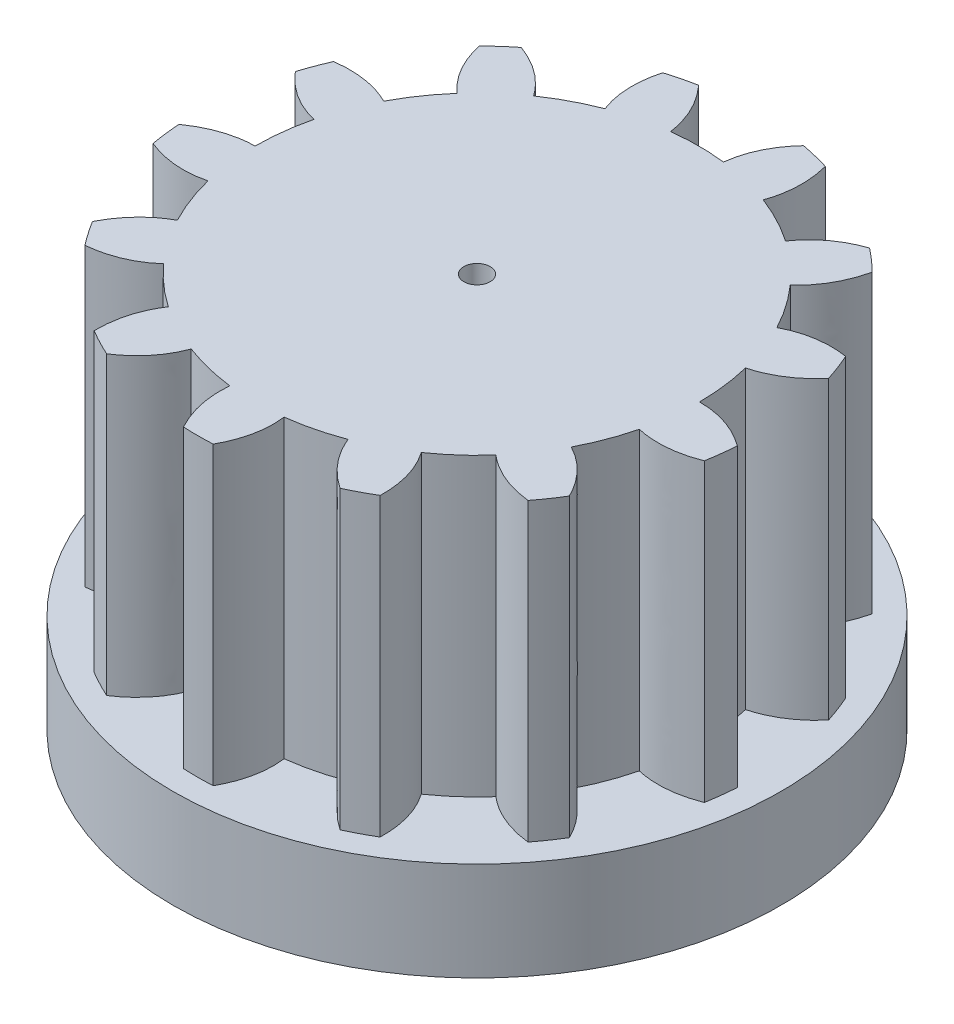
SolidWorks part; units mm, degrees
ref_plane "Front Plane" through (0, 0, 0) normal (0, 0, 1) x (1, 0, 0)
ref_plane "Top Plane" through (0, 0, 0) normal (0, 1, 0) x (1, 0, 0)
ref_plane "Right Plane" through (0, 0, 0) normal (1, 0, 0) x (0, 0, -1)
sketch "Sketch1" plane through (0, 0, 0) normal (0, 1, 0) x (1, 0, 0)
  line L0 (0, 0) -> (0, 17.0926) construction
  line L1 (0, 0) -> (3.5061, 14.2208) construction
  line L2 (0, 0) -> (1.9234, 15.8361) construction
  line L3 (0, 0) -> (4.6786, 12.3295) construction
  circle A3 centre (0, 0) radius 0.4
  arc A4 (-5.0652, 4.4616) -> (-5.9762, 3.138) centre (0, 0) ccw
  arc A6 (-2.4116, 6.3045) -> (-3.8334, 5.5559) centre (0, 0) ccw
  arc A7 (0.8138, 6.7008) -> (-0.8124, 6.7009) centre (0, 0) ccw
  arc A8 (3.8185, 5.5661) -> (2.3948, 6.3109) centre (0, 0) ccw
  arc A9 (5.9678, 3.154) -> (5.0533, 4.4751) centre (0, 0) ccw
  arc A10 (6.75, 0.0193) -> (6.5542, 1.6141) centre (0, 0) ccw
  arc A11 (5.9858, -3.1198) -> (6.5536, -1.6166) centre (0, 0) ccw
  arc A12 (3.8503, -5.5442) -> (5.0516, -4.477) centre (0, 0) ccw
  arc A13 (0.8328, -6.6984) -> (2.3924, -6.3118) centre (0, 0) ccw
  arc A14 (-2.3755, -6.3182) -> (-0.8149, -6.7006) centre (0, 0) ccw
  arc A15 (-5.0396, -4.4905) -> (-3.8355, -5.5544) centre (0, 0) ccw
  arc A16 (-6.5492, -1.6341) -> (-5.9774, -3.1358) centre (0, 0) ccw
  arc A17 (-6.5585, 1.5966) -> (-6.75, 0.0013) centre (0, 0) ccw
  arc A18 (-7.781, 3.4215) -> (-8.1003, 2.5759) centre (0, 0) ccw
  arc A19 (-8.4797, -0.5864) -> (-8.3695, -1.4836) centre (0, 0) ccw
  arc A20 (-7.2359, -4.46) -> (-6.7214, -5.2032) centre (0, 0) ccw
  arc A21 (-4.3344, -7.3118) -> (-3.5335, -7.7308) centre (0, 0) ccw
  arc A22 (-5.2996, 6.6456) -> (-5.9754, 6.0452) centre (0, 0) ccw
  arc A23 (-1.6043, 8.3472) -> (-2.4816, 8.1297) centre (0, 0) ccw
  arc A24 (8.3737, -1.46) -> (8.4814, -0.5625) centre (0, 0) ccw
  arc A25 (8.093, 2.5987) -> (7.7713, 3.4434) centre (0, 0) ccw
  arc A28 (2.4587, 8.1366) -> (1.5807, 8.3517) centre (0, 0) ccw
  arc A31 (5.9583, 6.062) -> (5.2809, 6.6605) centre (0, 0) ccw
  arc A32 (6.736, -5.1842) -> (7.2485, -4.4396) centre (0, 0) ccw
  arc A33 (3.5553, -7.7208) -> (4.355, -7.2996) centre (0, 0) ccw
  arc A34 (-0.44, -8.4886) -> (0.4639, -8.4873) centre (0, 0) ccw
  spline S0 degree 3 poles (0.633, 5.2117) (0.7252, 5.9828) (1.0144, 6.8191) (1.6201, 7.3229) knots 0 0 0 0 1 1 1 1 construction
  spline S1 degree 1 poles (1.6201, 7.3229) (1.9696, 7.2368) knots 0 0 1 1 construction
  spline S2 degree 3 poles (1.8622, 4.9086) (2.139, 5.6342) (2.2717, 6.5091) (1.9696, 7.2368) knots 0 0 0 0 1 1 1 1 construction
  spline S3 degree 3 poles (3.93, 3.481) (4.5123, 3.9948) (5.0364, 4.7079) (5.1071, 5.4925) knots 0 0 0 0 1 1 1 1 construction
  spline S4 degree 3 poles (2.9825, 4.3206) (3.4225, 4.9605) (4.0672, 5.5666) (4.8376, 5.7313) knots 0 0 0 0 1 1 1 1 construction
  spline S5 degree 1 poles (4.8376, 5.7313) (5.1071, 5.4925) knots 0 0 1 1 construction
  spline S6 degree 3 poles (5.0976, 1.2559) (5.852, 1.4403) (6.6474, 1.8281) (7.0746, 2.49) knots 0 0 0 0 1 1 1 1 construction
  spline S7 degree 3 poles (4.6487, 2.4397) (5.3357, 2.8018) (6.1883, 3.0389) (6.947, 2.8266) knots 0 0 0 0 1 1 1 1 construction
  spline S8 degree 1 poles (6.947, 2.8266) (7.0746, 2.49) knots 0 0 1 1 construction
  spline S9 degree 3 poles (5.0973, -1.2569) (5.851, -1.4442) (6.7355, -1.4705) (7.4214, -1.083) knots 0 0 0 0 1 1 1 1 construction
  spline S10 degree 3 poles (5.25, -0.0002) (6.0266, 0.0012) (6.8917, -0.1851) (7.4648, -0.7256) knots 0 0 0 0 1 1 1 1 construction
  spline S11 degree 1 poles (7.4648, -0.7256) (7.4214, -1.083) knots 0 0 1 1 construction
  spline S12 degree 3 poles (3.9293, -3.4818) (4.5096, -3.9979) (5.2806, -4.4322) (6.068, -4.4078) knots 0 0 0 0 1 1 1 1 construction
  spline S13 degree 3 poles (4.6486, -2.4399) (5.3369, -2.7996) (6.0163, -3.3666) (6.2726, -4.1115) knots 0 0 0 0 1 1 1 1 construction
  spline S14 degree 1 poles (6.2726, -4.1115) (6.068, -4.4078) knots 0 0 1 1 construction
  spline S15 degree 3 poles (1.8612, -4.909) (2.1351, -5.6357) (2.616, -6.3786) (3.3246, -6.7229) knots 0 0 0 0 1 1 1 1 construction
  spline S16 degree 3 poles (2.9822, -4.3208) (3.4245, -4.9591) (3.7626, -5.7769) (3.6434, -6.5556) knots 0 0 0 0 1 1 1 1 construction
  spline S17 degree 1 poles (3.6434, -6.5556) (3.3246, -6.7229) knots 0 0 1 1 construction
  spline S18 degree 3 poles (-0.6334, -5.2117) (-0.7285, -5.9824) (-0.6479, -6.8636) (-0.1805, -7.4978) knots 0 0 0 0 1 1 1 1 construction
  spline S19 degree 3 poles (0.6327, -5.2117) (0.7277, -5.9825) (0.647, -6.8637) (0.1795, -7.4979) knots 0 0 0 0 1 1 1 1 construction
  spline S20 degree 1 poles (0.1795, -7.4979) (-0.1805, -7.4978) knots 0 0 1 1 construction
  spline S21 degree 3 poles (-2.9828, -4.3204) (-3.4252, -4.9586) (-3.7634, -5.7764) (-3.6443, -6.5551) knots 0 0 0 0 1 1 1 1 construction
  spline S22 degree 3 poles (-1.8618, -4.9088) (-2.1359, -5.6354) (-2.6168, -6.3782) (-3.3255, -6.7224) knots 0 0 0 0 1 1 1 1 construction
  spline S23 degree 1 poles (-3.3255, -6.7224) (-3.6443, -6.5551) knots 0 0 1 1 construction
  spline S24 degree 3 poles (-4.6489, -2.4393) (-5.3372, -2.7989) (-6.0167, -3.3658) (-6.2731, -4.1107) knots 0 0 0 0 1 1 1 1 construction
  spline S25 degree 3 poles (-3.9298, -3.4813) (-4.5101, -3.9973) (-5.2812, -4.4315) (-6.0686, -4.407) knots 0 0 0 0 1 1 1 1 construction
  spline S26 degree 1 poles (-6.0686, -4.407) (-6.2731, -4.1107) knots 0 0 1 1 construction
  spline S27 degree 3 poles (-5.25, 0.0006) (-6.0266, 0.0021) (-6.8917, -0.1841) (-7.4649, -0.7246) knots 0 0 0 0 1 1 1 1 construction
  spline S28 degree 3 poles (-5.0975, -1.2563) (-5.8512, -1.4435) (-6.7357, -1.4696) (-7.4215, -1.082) knots 0 0 0 0 1 1 1 1 construction
  spline S29 degree 1 poles (-7.4215, -1.082) (-7.4649, -0.7246) knots 0 0 1 1 construction
  spline S30 degree 3 poles (-4.6484, 2.4403) (-5.3353, 2.8025) (-6.1879, 3.0397) (-6.9466, 2.8276) knots 0 0 0 0 1 1 1 1 construction
  spline S31 degree 3 poles (-5.0974, 1.2566) (-5.8518, 1.441) (-6.6471, 1.829) (-7.0743, 2.4909) knots 0 0 0 0 1 1 1 1 construction
  spline S32 degree 1 poles (-7.0743, 2.4909) (-6.9466, 2.8276) knots 0 0 1 1 construction
  spline S33 degree 3 poles (-2.9819, 4.321) (-3.4218, 4.9609) (-4.0665, 5.5672) (-4.8369, 5.7319) knots 0 0 0 0 1 1 1 1 construction
  spline S34 degree 3 poles (-3.9296, 3.4815) (-4.5118, 3.9954) (-5.0358, 4.7085) (-5.1064, 5.4932) knots 0 0 0 0 1 1 1 1 construction
  spline S35 degree 1 poles (-5.1064, 5.4932) (-4.8369, 5.7319) knots 0 0 1 1 construction
  spline S36 degree 3 poles (-0.6323, 5.2118) (-0.7244, 5.9829) (-1.0135, 6.8193) (-1.6191, 7.3232) knots 0 0 0 0 1 1 1 1 construction
  spline S37 degree 3 poles (-1.8615, 4.9089) (-2.1382, 5.6345) (-2.2708, 6.5094) (-1.9686, 7.237) knots 0 0 0 0 1 1 1 1 construction
  spline S38 degree 1 poles (-1.9686, 7.237) (-1.6191, 7.3232) knots 0 0 1 1 construction
  spline S39 degree 3 poles (-4.6484, 2.4403) (-4.4519, 2.8146) (-4.2099, 3.1651) (-3.9296, 3.4815) knots 0 0 0 0 0.038449 0.038449 0.038449 0.038449 construction
  spline S40 degree 3 poles (-2.9819, 4.321) (-2.6339, 4.5611) (-2.2568, 4.759) (-1.8615, 4.9089) knots 0.076923 0.076923 0.076923 0.076923 0.115372 0.115372 0.115372 0.115372 construction
  spline S41 degree 3 poles (-0.6323, 5.2118) (-0.2126, 5.2627) (0.2133, 5.2627) (0.633, 5.2117) (0.633, 5.2117) knots 0.153846 0.153846 0.153846 0.153846 0.192296 0.192296 0.192296 0.192296 0.192296 construction
  spline S42 degree 3 poles (-5.25, 0.0006) (-5.25, 0.4233) (-5.1986, 0.8461) (-5.0974, 1.2566) knots 0.923077 0.923077 0.923077 0.923077 0.961526 0.961526 0.961526 0.961526 construction
  spline S43 degree 3 poles (-4.6489, -2.4393) (-4.8453, -2.0649) (-4.9963, -1.6667) (-5.0975, -1.2563) knots 0.846154 0.846154 0.846154 0.846154 0.884603 0.884603 0.884603 0.884603 construction
  spline S44 degree 3 poles (-2.9828, -4.3204) (-3.3307, -4.0802) (-3.6494, -3.7977) (-3.9298, -3.4813) knots 0.769231 0.769231 0.769231 0.769231 0.80768 0.80768 0.80768 0.80768 construction
  spline S45 degree 3 poles (-0.6334, -5.2117) (-1.053, -5.1607) (-1.4665, -5.0587) (-1.8618, -4.9088) knots 0.692308 0.692308 0.692308 0.692308 0.730757 0.730757 0.730757 0.730757 construction
  spline S46 degree 3 poles (1.8612, -4.909) (1.4659, -5.0589) (1.0524, -5.1608) (0.6327, -5.2117) knots 0.615385 0.615385 0.615385 0.615385 0.653834 0.653834 0.653834 0.653834 construction
  spline S47 degree 3 poles (3.9293, -3.4818) (3.6489, -3.7982) (3.3302, -4.0806) (2.9822, -4.3208) knots 0.538462 0.538462 0.538462 0.538462 0.576911 0.576911 0.576911 0.576911 construction
  spline S48 degree 3 poles (5.0973, -1.2569) (4.9961, -1.6674) (4.8451, -2.0656) (4.6486, -2.4399) knots 0.461538 0.461538 0.461538 0.461538 0.499988 0.499988 0.499988 0.499988 construction
  spline S49 degree 3 poles (5.0976, 1.2559) (5.1987, 0.8454) (5.25, 0.4226) (5.25, -0.0002) knots 0.384615 0.384615 0.384615 0.384615 0.423065 0.423065 0.423065 0.423065 construction
  spline S50 degree 3 poles (3.93, 3.481) (4.2104, 3.1645) (4.4523, 2.814) (4.6487, 2.4397) knots 0.307692 0.307692 0.307692 0.307692 0.346142 0.346142 0.346142 0.346142 construction
  spline S51 degree 3 poles (1.8622, 4.9086) (2.2575, 4.7587) (2.6345, 4.5607) (2.9825, 4.3206) knots 0.230769 0.230769 0.230769 0.230769 0.269219 0.269219 0.269219 0.269219 construction
  spline S52 degree 3 poles (0.7945, 6.7031) (0.8653, 7.3126) (1.1274, 7.8622) (1.5807, 8.3517) knots 0 0 0 0 0.872429 0.872429 0.872429 0.872429
  spline S53 degree 3 poles (2.4587, 8.1366) (2.623, 7.4967) (2.6017, 6.8881) (2.3948, 6.3109) knots 0.127683 0.127683 0.127683 0.127683 1 1 1 1
  spline S54 degree 3 poles (3.8185, 5.5661) (4.1646, 6.0729) (4.652, 6.4377) (5.2809, 6.6605) knots 0 0 0 0 0.872429 0.872429 0.872429 0.872429
  spline S55 degree 3 poles (5.9583, 6.062) (5.8065, 5.419) (5.5048, 4.89) (5.0533, 4.4751) knots 0.127683 0.127683 0.127683 0.127683 1 1 1 1
  spline S56 degree 3 poles (5.9678, 3.154) (6.5097, 3.4419) (7.1109, 3.5384) (7.7713, 3.4434) knots 0 0 0 0 0.872429 0.872429 0.872429 0.872429
  spline S57 degree 3 poles (8.093, 2.5987) (7.6597, 2.0999) (7.1468, 1.7717) (6.5542, 1.6141) knots 0.127683 0.127683 0.127683 0.127683 1 1 1 1
  spline S58 degree 3 poles (6.75, 0.0193) (7.3636, 0.0224) (7.9407, -0.1715) (8.4814, -0.5625) knots 0 0 0 0 0.872429 0.872429 0.872429 0.872429
  spline S59 degree 3 poles (8.3737, -1.46) (7.7582, -1.7003) (7.1515, -1.7525) (6.5536, -1.6166) knots 0.127683 0.127683 0.127683 0.127683 1 1 1 1
  spline S60 degree 3 poles (5.9858, -3.1198) (6.5306, -3.4022) (6.9515, -3.8421) (7.2485, -4.4396) knots 0 0 0 0 0.872429 0.872429 0.872429 0.872429
  spline S61 degree 3 poles (6.736, -5.1842) (6.0794, -5.1109) (5.5179, -4.8752) (5.0516, -4.477) knots 0.127683 0.127683 0.127683 0.127683 1 1 1 1
  spline S62 degree 3 poles (3.8503, -5.5442) (4.2015, -6.0474) (4.3697, -6.6325) (4.355, -7.2996) knots 0 0 0 0 0.872429 0.872429 0.872429 0.872429
  spline S63 degree 3 poles (3.5553, -7.7208) (3.0079, -7.3508) (2.6202, -6.8811) (2.3924, -6.3118) knots 0.127683 0.127683 0.127683 0.127683 1 1 1 1
  spline S64 degree 3 poles (0.8328, -6.6984) (0.9098, -7.3072) (0.7869, -7.9035) (0.4639, -8.4873) knots 0 0 0 0 0.872429 0.872429 0.872429 0.872429
  spline S65 degree 3 poles (-0.44, -8.4886) (-0.7527, -7.9066) (-0.8777, -7.3106) (-0.8149, -6.7006) knots 0.127683 0.127683 0.127683 0.127683 1 1 1 1
  spline S66 degree 3 poles (-2.3755, -6.3182) (-2.5902, -6.8931) (-2.9762, -7.3639) (-3.5335, -7.7308) knots 0 0 0 0 0.872429 0.872429 0.872429 0.872429
  spline S67 degree 3 poles (-4.3344, -7.3118) (-4.3409, -6.6511) (-4.1746, -6.0653) (-3.8355, -5.5544) knots 0.127683 0.127683 0.127683 0.127683 1 1 1 1
  spline S68 degree 3 poles (-5.0396, -4.4905) (-5.4969, -4.8998) (-6.0575, -5.1373) (-6.7214, -5.2032) knots 0 0 0 0 0.872429 0.872429 0.872429 0.872429
  spline S69 degree 3 poles (-7.2359, -4.46) (-6.9346, -3.872) (-6.5151, -3.4306) (-5.9774, -3.1358) knots 0.127683 0.127683 0.127683 0.127683 1 1 1 1
  spline S70 degree 3 poles (-6.5492, -1.6341) (-7.1443, -1.784) (-7.751, -1.7338) (-8.3695, -1.4836) knots 0 0 0 0 0.872429 0.872429 0.872429 0.872429
  spline S71 degree 3 poles (-8.4797, -0.5864) (-7.9397, -0.2058) (-7.3631, -0.0099) (-6.75, 0.0013) knots 0.127683 0.127683 0.127683 0.127683 1 1 1 1
  spline S72 degree 3 poles (-6.5585, 1.5966) (-7.155, 1.7405) (-7.669, 2.0669) (-8.1003, 2.5759) knots 0 0 0 0 0.872429 0.872429 0.872429 0.872429
  spline S73 degree 3 poles (-7.781, 3.4215) (-7.1259, 3.5075) (-6.5243, 3.413) (-5.9762, 3.138) knots 0.127683 0.127683 0.127683 0.127683 1 1 1 1
  spline S74 degree 3 poles (-5.0652, 4.4616) (-5.5266, 4.8662) (-5.83, 5.3941) (-5.9754, 6.0452) knots 0 0 0 0 0.872429 0.872429 0.872429 0.872429
  spline S75 degree 3 poles (-5.2996, 6.6456) (-4.6796, 6.4173) (-4.1909, 6.0541) (-3.8334, 5.5559) knots 0.127683 0.127683 0.127683 0.127683 1 1 1 1
  spline S76 degree 3 poles (-2.4116, 6.3045) (-2.6321, 6.8771) (-2.6555, 7.4855) (-2.4816, 8.1297) knots 0 0 0 0 0.872429 0.872429 0.872429 0.872429
  spline S77 degree 3 poles (-1.6043, 8.3472) (-1.1613, 7.857) (-0.8973, 7.3082) (-0.8124, 6.7009) knots 0.127683 0.127683 0.127683 0.127683 1 1 1 1
  point P62 (1.792, 8.5633)
  point P64 (0, 0)
  point P66 (2.3745, 8.4197)
  point P121 (0, 0)
  dimension "D2" = 13.5
  dimension "D3" = 0.31
  dimension "D4" = 0.8
  dimension "D9" = 17
  dimension "D5" = 13.85
  dimension "D6" = 6.925
  dimension "D7" = 6.93
  dimension "D8" = 0.6
extrude "Boss-Extrude1" add sketch "Sketch1" along normal blind 9
sketch "Sketch2" plane through (0, 0, 0) normal (0, -1, 0) x (1, 0, 0)
  circle A1 centre (0, 0) radius 9.25
  dimension "D1" = 18.5
extrude "Boss-Extrude2" add sketch "Sketch2" along normal blind 3
